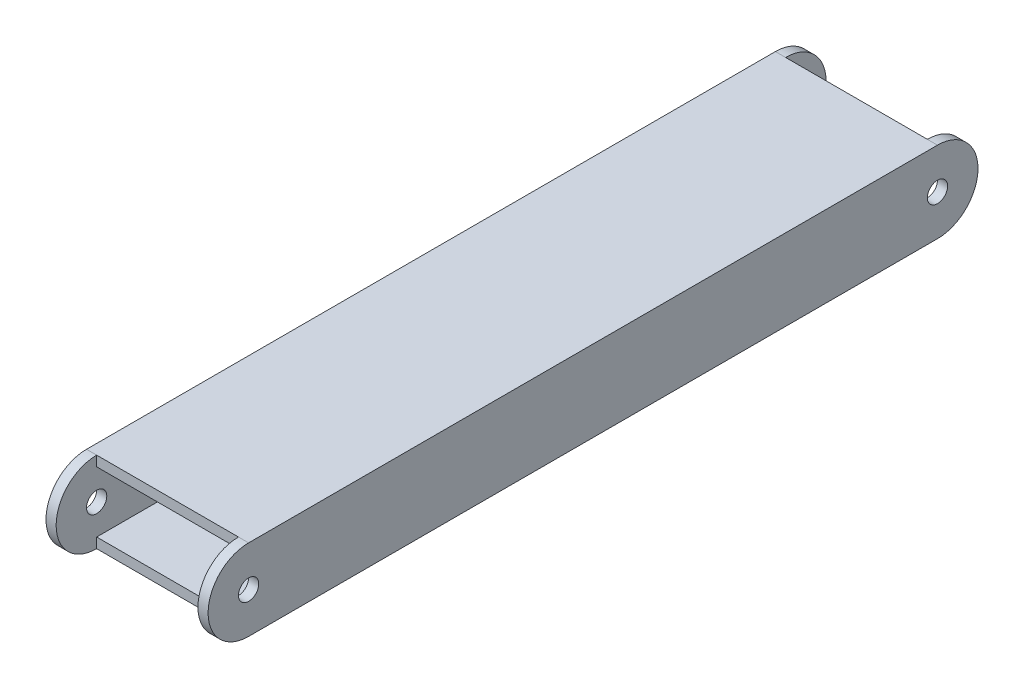
SolidWorks part; units mm, degrees
material "6061-T6 (SS)"
ref_plane "Front Plane" through (0, 0, 0) normal (0, 0, 1) x (1, 0, 0)
ref_plane "Top Plane" through (0, 0, 0) normal (0, 1, 0) x (1, 0, 0)
ref_plane "Right Plane" through (0, 0, 0) normal (1, 0, 0) x (0, 0, -1)
sketch "Link2OuterLip" plane through (0, 0, 0) normal (0, 0, 1) x (1, 0, 0)
  line L1 (-25.4, -12.7) -> (25.4, -12.7)
  line L2 (-25.4, -12.7) -> (-25.4, 12.7)
  line L3 (-25.4, 12.7) -> (25.4, 12.7)
  line L4 (25.4, -12.7) -> (25.4, 12.7)
  line L5 (-25.4, -12.7) -> (25.4, 12.7) construction
  line L6 (-25.4, 12.7) -> (25.4, -12.7) construction
  point P0 (0, 0)
  dimension "D1" = 25.4
  dimension "D2" = 50.8
extrude "Extrude-Thin1" add sketch "Link2OuterLip" along normal blind 215.9 thin thin type one direction reverse wall 3.175
sketch "Sketch2" plane through (-25.4, 0, 0) normal (-1, 0, 0) x (0, 0, 1)
  line L0 (0, 12.7) -> (0, -12.7) construction
  line L1 (0, -12.7) -> (0, 12.7)
  arc A0 (0, 12.7) -> (0, -12.7) centre (0, 0) ccw
extrude "Boss-Extrude1" add sketch "Sketch2" against normal up to surface (3.175 mm away) up to face at (-22.225, 0, 107.95)
sketch "Sketch3" plane through (25.4, 0, 0) normal (1, 0, 0) x (0, 0, -1)
  line L0 (0, 12.7) -> (0, -12.7)
  arc A1 (0, -12.7) -> (0, 12.7) centre (0, 0) ccw
extrude "Boss-Extrude2" add sketch "Sketch3" against normal up to surface (3.175 mm away) up to face at (22.225, 0, 107.95)
sketch "Sketch4" plane through (25.4, 0, 0) normal (1, 0, 0) x (0, 0, -1)
  circle A0 centre (0, 0) radius 3.175
extrude "Cut-Extrude1" cut sketch "Sketch4" against normal up to surface (50.8 mm away) up to face at (-25.4, 0, 104.775)
ref_plane "Plane1" through (0, 0, 107.95) normal (0, 0, 1) x (1, 0, 0)
mirror "Mirror1" about plane through (0, 0, 107.95) normal (0, 0, 1) of "Boss-Extrude1", "Boss-Extrude2", "Cut-Extrude1"
